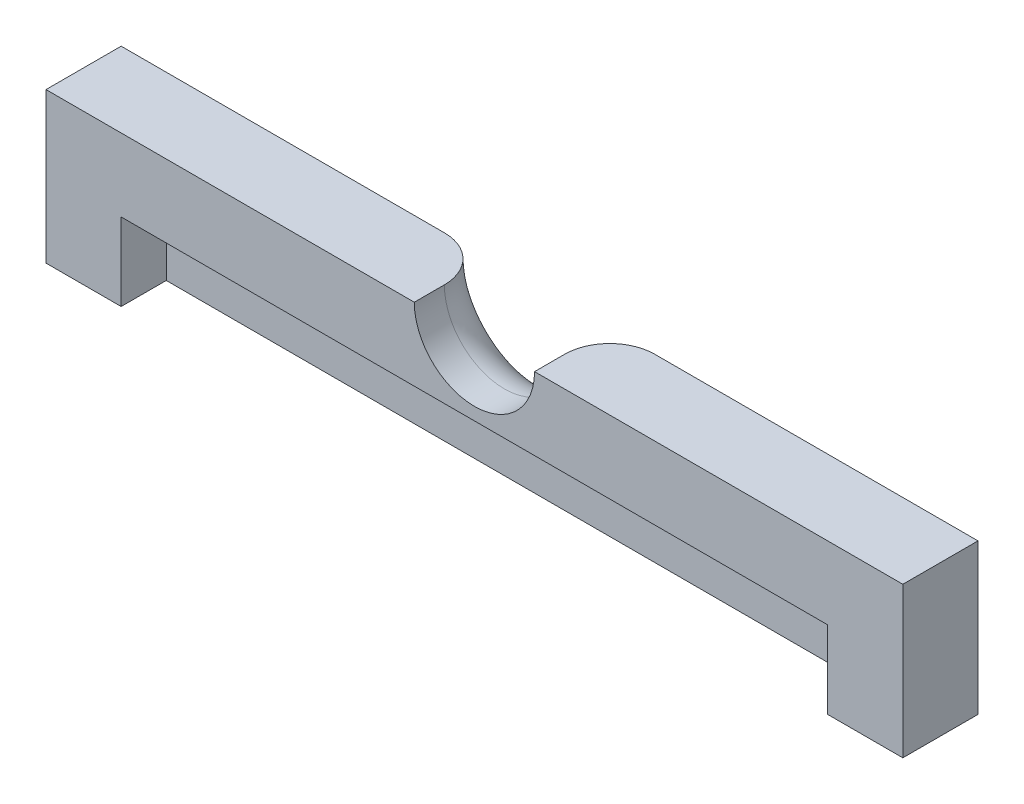
SolidWorks part; units mm, degrees
ref_plane "Front Plane" through (0, 0, 0) normal (0, 0, 1) x (1, 0, 0)
ref_plane "Top Plane" through (0, 0, 0) normal (0, 1, 0) x (1, 0, 0)
ref_plane "Right Plane" through (0, 0, 0) normal (1, 0, 0) x (0, 0, -1)
sketch "Sketch1" plane through (0, 0, 0) normal (0, 0, 1) x (1, 0, 0)
  line L1 (0, 0) -> (57, 0)
  line L2 (0, 0) -> (0, -10)
  line L3 (0, -10) -> (57, -10)
  line L4 (57, 0) -> (57, -10)
  dimension "D1" = 57
  dimension "D2" = 10
extrude "Boss-Extrude1" add sketch "Sketch1" along normal blind 5
sketch "Sketch2" plane through (0, 0, 5) normal (0, 0, 1) x (1, 0, 0)
  line L0 (0, -10) -> (57, -10) construction
  line L1 (5, -10) -> (52, -10)
  line L2 (5, -10) -> (5, -4.8377)
  line L3 (5, -4.8377) -> (52, -4.8377)
  line L4 (52, -10) -> (52, -4.8377)
extrude "Cut-Extrude1" cut sketch "Sketch2" against normal blind 3
sketch "Sketch3" plane through (0, 0, 0) normal (0, 0, -1) x (-1, 0, 0)
  line L0 (-57, 0) -> (0, 0) construction
  line L1 (-32.5, 0) -> (-24.5, 0)
  arc A0 (-32.5, 0) -> (-24.5, 0) centre (-28.5, 0) ccw
  dimension "D1" = 8
extrude "Cut-Extrude2" cut sketch "Sketch3" against normal through all
fillet "Fillet1" radius 3 1 edges at (28.5, -4, 0)
